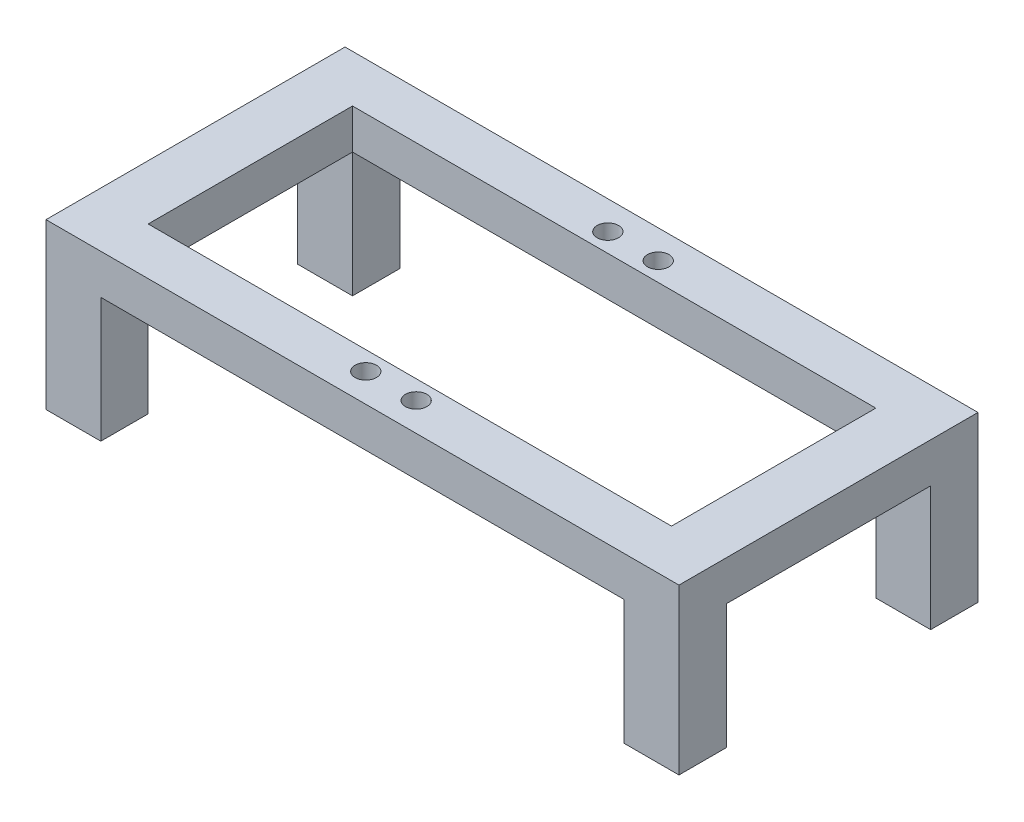
SolidWorks part; units mm, degrees
material "ABS"
ref_plane "Front Plane" through (0, 0, 0) normal (0, 0, 1) x (1, 0, 0)
ref_plane "Top Plane" through (0, 0, 0) normal (0, 1, 0) x (1, 0, 0)
ref_plane "Right Plane" through (0, 0, 0) normal (1, 0, 0) x (0, 0, -1)
sketch "Sketch2" plane through (0, 0, 0) normal (0, 1, 0) x (1, 0, 0)
  line L1 (-63.5, 30) -> (63.5, 30)
  line L2 (-63.5, 30) -> (-63.5, -30)
  line L3 (-63.5, -30) -> (63.5, -30)
  line L4 (63.5, 30) -> (63.5, -30)
  line L5 (-63.5, 30) -> (63.5, -30) construction
  line L6 (-63.5, -30) -> (63.5, 30) construction
  line L7 (-52.5, 20.5) -> (52.5, 20.5)
  line L8 (-52.5, 20.5) -> (-52.5, -20.5)
  line L9 (-52.5, -20.5) -> (52.5, -20.5)
  line L10 (52.5, 20.5) -> (52.5, -20.5)
  line L11 (-52.5, 20.5) -> (52.5, -20.5) construction
  line L12 (-52.5, -20.5) -> (52.5, 20.5) construction
  point P1 (0, 0)
  dimension "D1" = 41
  dimension "D2" = 60
  dimension "D3" = 127
  dimension "D4" = 105
extrude "Boss-Extrude2" add sketch "Sketch2" against normal blind 8
sketch "Sketch3" plane through (0, 0, 0) normal (0, 1, 0) x (1, 0, 0)
  line L0 (-5.055, 24.285) -> (5.055, -24.285) construction
  line L1 (-5.055, 24.285) -> (5.055, 24.285) construction
  line L2 (-5.055, 24.285) -> (-5.055, -24.285) construction
  line L3 (-5.055, -24.285) -> (5.055, -24.285) construction
  line L4 (5.055, 24.285) -> (5.055, -24.285) construction
  line L5 (-5.055, -24.285) -> (5.055, 24.285) construction
  circle A0 centre (5.055, -24.285) radius 2.15
  circle A1 centre (-5.055, 24.285) radius 2.15
  circle A2 centre (5.055, 24.285) radius 2.15
  circle A3 centre (-5.055, -24.285) radius 2.15
  point P4 (0, 0)
  dimension "D3" = 4.3
  dimension "D1" = 48.57
  dimension "D2" = 10.11
extrude "Cut-Extrude1" cut sketch "Sketch3" against normal blind 5.1594 contours A0 | A3 | A2 | A1
sketch "Sketch4" plane through (0, -8, 0) normal (0, -1, 0) x (1, 0, 0)
  line L0 (-63.5, -30) -> (-63.5, 30) construction
  line L1 (-63.5, 30) -> (-52.5, 30)
  line L2 (-63.5, 30) -> (-63.5, 20.5)
  line L3 (-63.5, 20.5) -> (-52.5, 20.5)
  line L4 (-52.5, 30) -> (-52.5, 20.5)
  line L5 (-63.5, 30) -> (63.5, 30) construction
  line L6 (-52.5, -20.5) -> (-52.5, 20.5) construction
  line L7 (-52.5, 20.5) -> (52.5, 20.5) construction
  line L8 (0, -4.4) -> (0, 4.4) construction
  line L9 (63.5, 20.5) -> (52.5, 20.5)
  line L10 (63.5, 30) -> (63.5, 20.5)
  line L11 (63.5, 30) -> (52.5, 30)
  line L12 (52.5, 30) -> (52.5, 20.5)
  line L13 (4.4, 0) -> (-4.4, 0) construction
  line L14 (63.5, -30) -> (63.5, -20.5)
  line L15 (63.5, -30) -> (52.5, -30)
  line L16 (52.5, -30) -> (52.5, -20.5)
  line L17 (63.5, -20.5) -> (52.5, -20.5)
  line L18 (-63.5, -20.5) -> (-52.5, -20.5)
  line L19 (-63.5, -30) -> (-63.5, -20.5)
  line L20 (-63.5, -30) -> (-52.5, -30)
  line L21 (-52.5, -30) -> (-52.5, -20.5)
  point P6 (-63.5, 29.4139)
  point P9 (-52.5, 20.5)
extrude "Boss-Extrude3" add sketch "Sketch4" along normal blind 25
